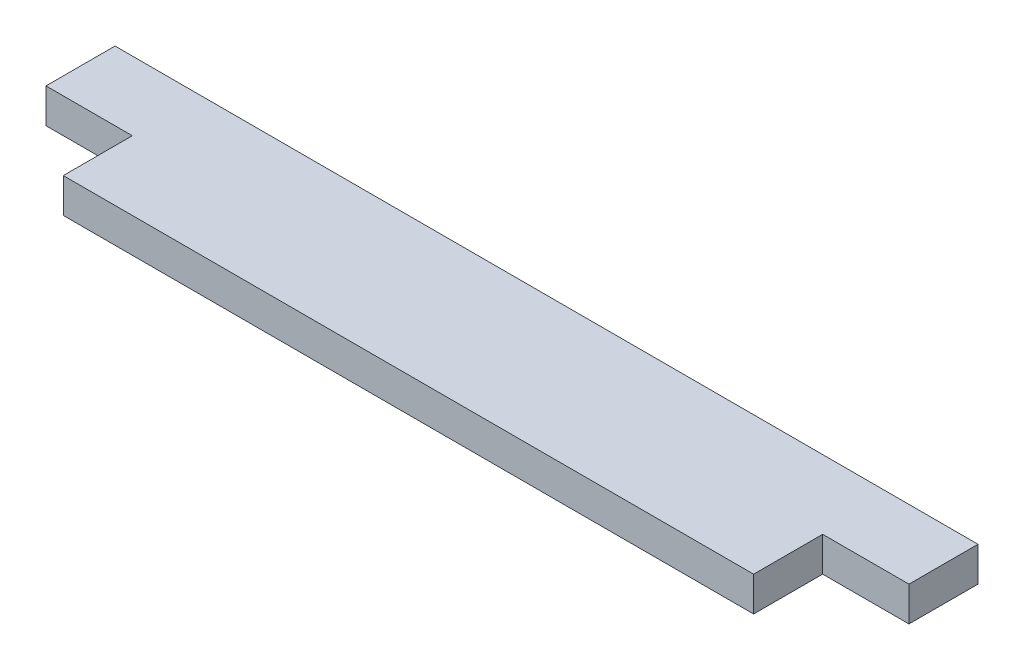
SolidWorks part; units mm, degrees
ref_plane "Front Plane" through (0, 0, 0) normal (0, 0, 1) x (1, 0, 0)
ref_plane "Top Plane" through (0, 0, 0) normal (0, 1, 0) x (1, 0, 0)
ref_plane "Right Plane" through (0, 0, 0) normal (1, 0, 0) x (0, 0, -1)
sketch "Sketch1" plane through (0, 0, 0) normal (0, 1, 0) x (1, 0, 0)
  line L1 (-7.2586, 1.7069) -> (42.7414, 1.7069)
  line L2 (-7.2586, 1.7069) -> (-7.2586, -2.2931)
  line L3 (-7.2586, -2.2931) -> (42.7414, -2.2931)
  line L4 (42.7414, 1.7069) -> (42.7414, -2.2931)
  line L5 (-2.2586, -2.2931) -> (37.7414, -2.2931)
  line L6 (-2.2586, -2.2931) -> (-2.2586, -6.2931)
  line L7 (-2.2586, -6.2931) -> (37.7414, -6.2931)
  line L8 (37.7414, -2.2931) -> (37.7414, -6.2931)
  dimension "D1" = 4
  dimension "D2" = 50
  dimension "D3" = 4
  dimension "D4" = 40
  dimension "D5" = 5
extrude "Boss-Extrude1" add sketch "Sketch1" along normal blind 2 contours L4 L1 L2 L3 | L8 L3 L6 L7
